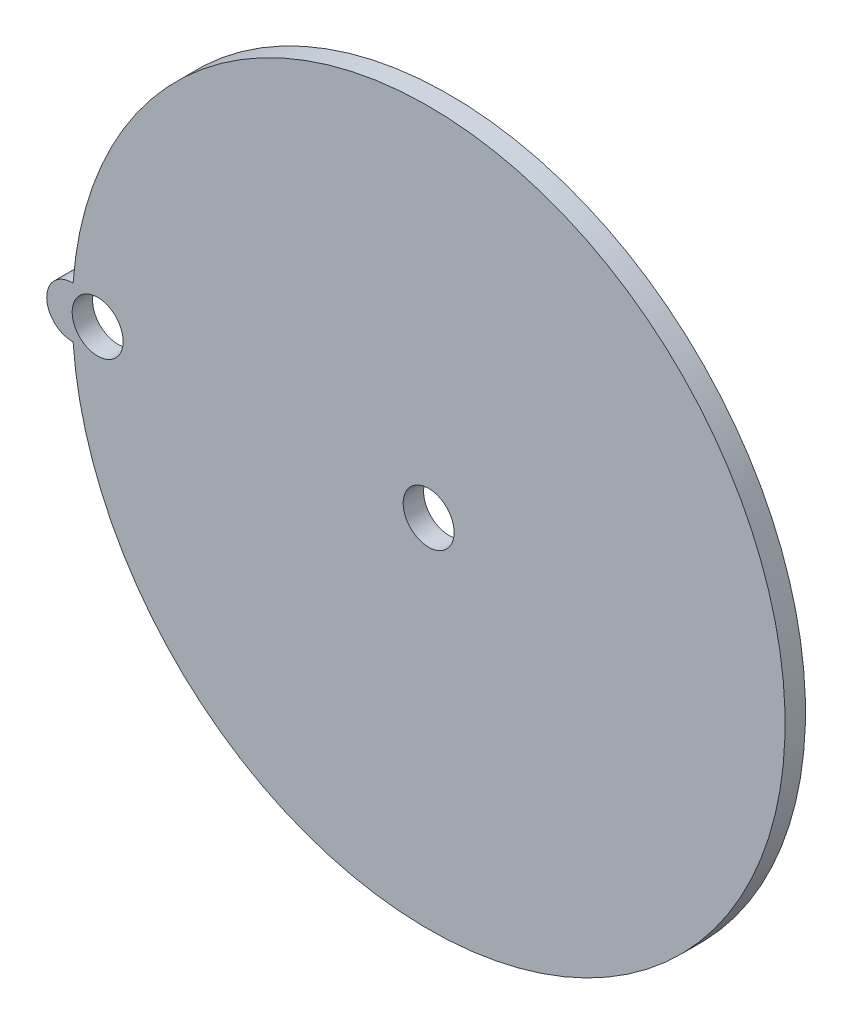
SolidWorks part; units mm, degrees
ref_plane "Front" through (0, 0, 0) normal (0, 0, 1) x (1, 0, 0)
ref_plane "Top" through (0, 0, 0) normal (0, 1, 0) x (1, 0, 0)
ref_plane "Right" through (0, 0, 0) normal (1, 0, 0) x (0, 0, -1)
sketch "Sketch2" plane through (0, 0, 0) normal (0, 0, 1) x (1, 0, 0)
  circle A0 centre (0, 0) radius 44.45
  circle A1 centre (-41.275, 0) radius 3.175
  arc A2 (-44.3366, -3.173) -> (-44.3366, 3.173) centre (-44.45, 0) cw
  circle A3 centre (0, 0) radius 3.175
  dimension "D1" = 6.35
  dimension "D2" = 88.9
  dimension "D3" = 3.175
extrude "Boss-Extrude2" add sketch "Sketch2" along normal blind 2.54 contours A0 A1 | A2 A0
